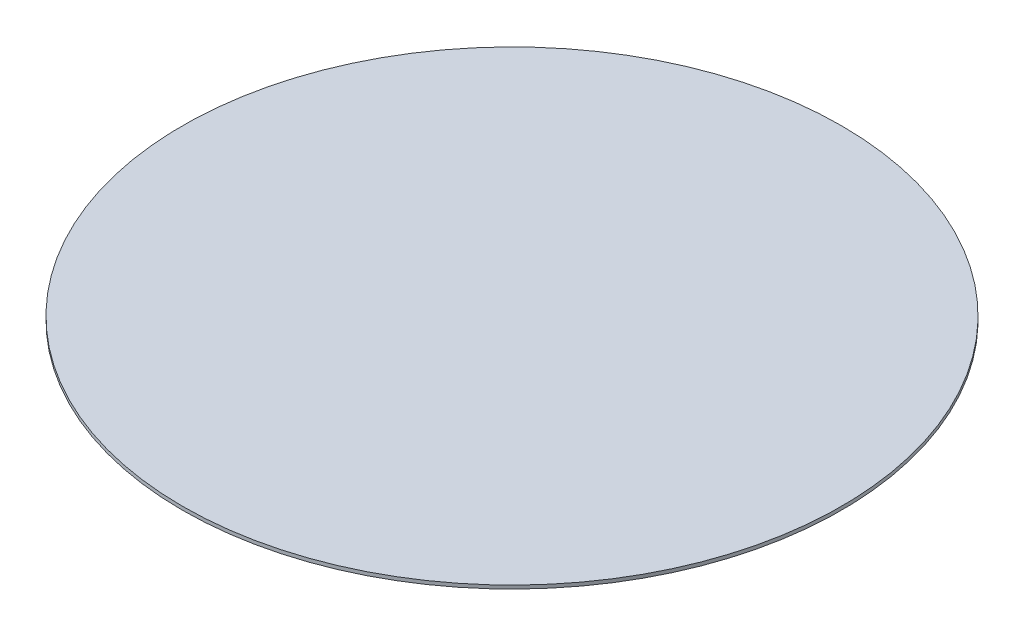
SolidWorks part; units mm, degrees
ref_plane "Piano frontale" through (0, 0, 0) normal (0, 0, 1) x (1, 0, 0)
ref_plane "Piano superiore" through (0, 0, 0) normal (0, 1, 0) x (1, 0, 0)
ref_plane "Piano destro" through (0, 0, 0) normal (1, 0, 0) x (0, 0, -1)
sketch "Schizzo1" plane through (0, 0, 0) normal (0, 1, 0) x (1, 0, 0)
  circle A0 centre (0, 0) radius 9.5
extrude "Estrusione-Estrusione1" add sketch "Schizzo1" along normal blind 0.1
